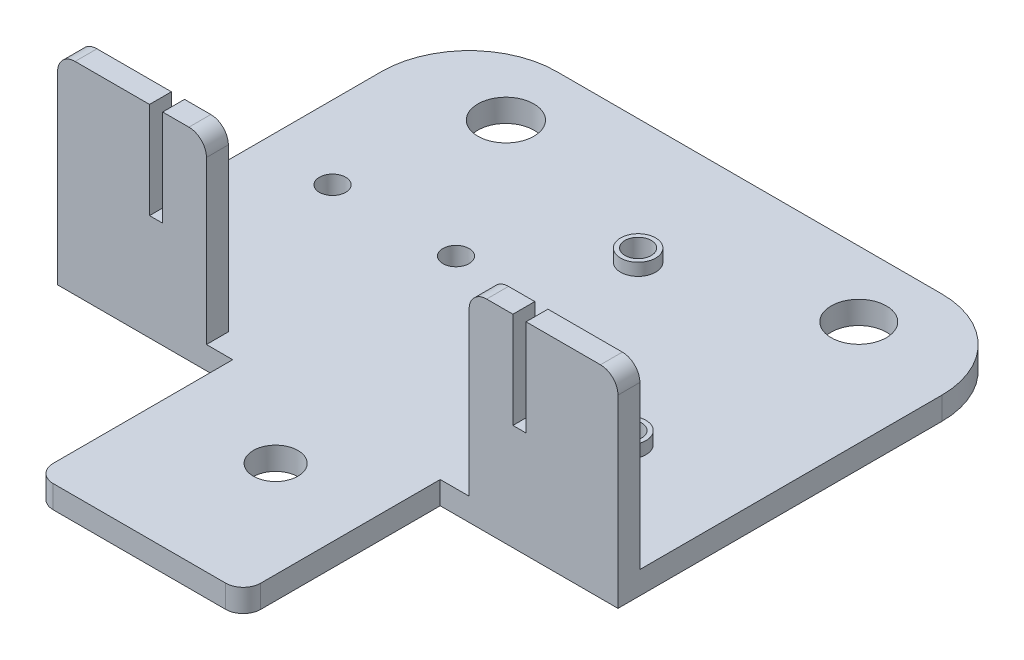
SolidWorks part; units mm, degrees
ref_plane "Front Plane" through (0, 0, 0) normal (0, 0, 1) x (1, 0, 0)
ref_plane "Top Plane" through (0, 0, 0) normal (0, 1, 0) x (1, 0, 0)
ref_plane "Right Plane" through (0, 0, 0) normal (1, 0, 0) x (0, 0, -1)
sketch "Sketch1" plane through (0, 0, 0) normal (0, 1, 0) x (1, 0, 0)
  line L0 (11.7, -23.5) -> (32, -23.5)
  line L1 (-32, -23.5) -> (-12, -23.5)
  line L2 (-32, -23.5) -> (-32, 13.5)
  line L3 (-22, 23.5) -> (22, 23.5)
  line L4 (32, -23.5) -> (32, 13.5)
  line L5 (-32, -23.5) -> (32, 23.5) construction
  line L6 (-32, 23.5) -> (32, -23.5) construction
  line L8 (-12, -23.5) -> (-12, -46)
  line L9 (-12, -46) -> (11.7, -46)
  line L10 (11.7, -23.5) -> (11.7, -46)
  arc A0 (-32, 13.5) -> (-22, 23.5) centre (-22, 13.5) cw
  arc A1 (32, 13.5) -> (22, 23.5) centre (22, 13.5) ccw
  point P0 (0, 0)
  dimension "D6" = 10
  dimension "D7" = 10
  dimension "D1" = 64
  dimension "D2" = 47
  dimension "D3" = 20
  dimension "D4" = 23.7
  dimension "D5" = 22.5
extrude "Main Body" add sketch "Sketch1" along normal blind 2.6
sketch "Sketch5" plane through (0, 2.6, 0) normal (0, 1, 0) x (1, 0, 0)
  line L0 (32, -23.5) -> (32, 13.5) construction
  line L1 (11.7, -23.5) -> (32, -23.5) construction
  line L2 (22, 23.5) -> (-22, 23.5) construction
  line L3 (-32, 13.5) -> (-32, -23.5) construction
  circle A0 centre (19, -9.3) radius 2
  circle A1 centre (1.5, 9.3) radius 2
  dimension "D1" = 4
  dimension "D2" = 4
  dimension "D3" = 13
  dimension "D4" = 14.2
  dimension "D5" = 33.5
  dimension "D6" = 14.2
sketch "Sketch2" plane through (0, 2.6, 0) normal (0, 1, 0) x (1, 0, 0)
  line L0 (22, 23.5) -> (-22, 23.5) construction
  line L1 (-32, 13.5) -> (-32, -23.5) construction
  line L3 (32, -23.5) -> (32, 13.5) construction
  line L4 (-32, -23.5) -> (-12, -23.5) construction
  line L5 (11.7, -23.5) -> (32, -23.5) construction
  line L6 (-12, -23.5) -> (-12, -46) construction
  line L7 (-12, -46) -> (11.7, -46) construction
  circle A0 centre (-20.1, 15.8) radius 3.2
  circle A1 centre (20, 16) radius 3.15
  circle A2 centre (1.5, 9.3) radius 1.5
  circle A3 centre (-23.6, -0.5) radius 1.5
  circle A4 centre (-9.5, -0.5) radius 1.5
  circle A5 centre (19, -9.3) radius 1.5
  circle A6 centre (0.7, -31.3) radius 2.55
  point P20 (20, -10.9351)
  point P21 (-7.2502, -13.8289)
  dimension "D1" = 6.4
  dimension "D4" = 6.3
  dimension "D7" = 3
  dimension "D8" = 3
  dimension "D9" = 3
  dimension "D10" = 3
  dimension "D11" = 5.1
  dimension "D2" = 7.7
  dimension "D3" = 11.9
  dimension "D5" = 7.5
  dimension "D6" = 12
  dimension "D12" = 8.4
  dimension "D13" = 23
  dimension "D14" = 22.5
  dimension "D15" = 23
  dimension "D16" = 14.2
  dimension "D17" = 33.5
  dimension "D18" = 13
  dimension "D19" = 14.2
  dimension "D20" = 12.7
  dimension "D21" = 14.7
sketch "Sketch4" plane through (0, 2.6, 0) normal (0, 1, 0) x (1, 0, 0)
  line L1 (-32, -23.5) -> (-15, -23.5)
  line L2 (-32, -23.5) -> (-32, -21)
  line L3 (-32, -21) -> (-15, -21)
  line L4 (-15, -23.5) -> (-15, -21)
  line L5 (32, -23.5) -> (15, -23.5)
  line L6 (32, -23.5) -> (32, -21)
  line L7 (32, -21) -> (15, -21)
  line L8 (15, -23.5) -> (15, -21)
  dimension "D1" = 2.5
  dimension "D2" = 2.5
  dimension "D3" = 17
  dimension "D4" = 17
extrude "Flanges" add sketch "Sketch4" along normal blind 20.5
extrude "Drill hold extrude" add sketch "Sketch5" along normal blind 1.4
extrude "Screw holes" cut sketch "Sketch2" against normal through all both and the other way through all
fillet "Flange Fillet" radius 2 4 edges at (32, 23.1, 22.25) (15, 23.1, 22.25) (-15, 23.1, 22.25) (-32, 23.1, 22.25)
sketch "Sketch6" plane through (0, 0, 21) normal (0, 0, -1) x (-1, 0, 0)
  line L0 (17, 23.1) -> (30, 23.1) construction
  line L1 (-21.5, 23.1) -> (-20, 23.1)
  line L2 (-21.5, 23.1) -> (-21.5, 12.1)
  line L3 (-21.5, 12.1) -> (-20, 12.1)
  line L4 (-20, 23.1) -> (-20, 12.1)
  line L6 (-30, 23.1) -> (-17, 23.1) construction
  line L7 (20, 23.1) -> (21.5, 23.1)
  line L8 (20, 23.1) -> (20, 12.1)
  line L9 (20, 12.1) -> (21.5, 12.1)
  line L10 (21.5, 23.1) -> (21.5, 12.1)
  line L11 (-15, 21.1) -> (-15, 2.6) construction
  line L12 (15, 21.1) -> (15, 2.6) construction
  point P6 (-20.75, 12.1)
  point P15 (22.5234, 9.78)
  dimension "D1" = 11
  dimension "D2" = 5
  dimension "D3" = 6.5
  dimension "D4" = 5
  dimension "D5" = 6.5
  dimension "D6" = 11
extrude "Flange Notches" cut sketch "Sketch6" against normal through all
fillet "Main lower body Fillet" radius 2 2 edges at (11.7, 1.3, 46) (-12, 1.3, 46)
